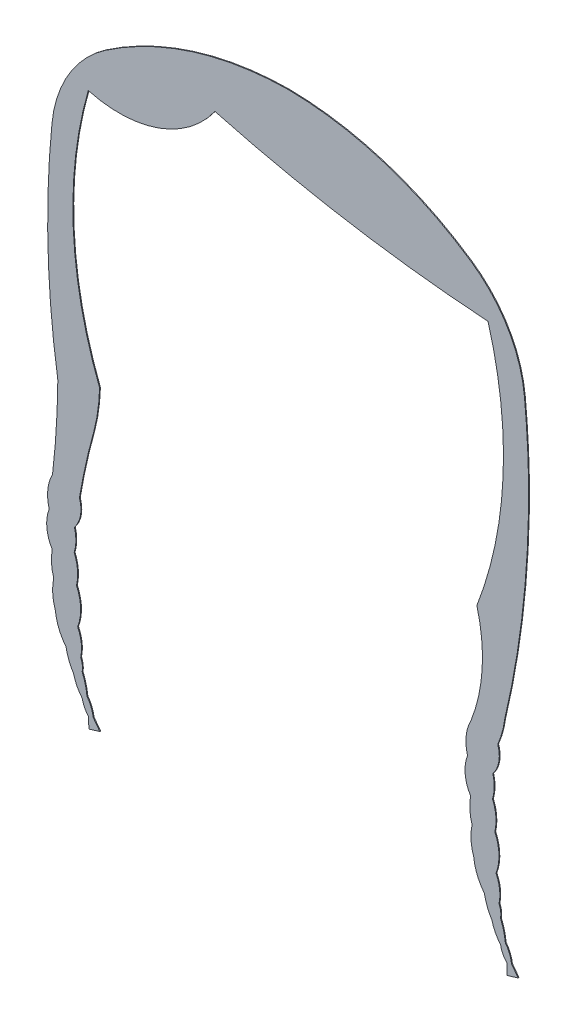
SolidWorks part; units mm, degrees
ref_plane "Alzado" through (0, 0, 0) normal (0, 0, 1) x (1, 0, 0)
ref_plane "Planta" through (0, 0, 0) normal (0, 1, 0) x (1, 0, 0)
ref_plane "Vista lateral" through (0, 0, 0) normal (1, 0, 0) x (0, 0, -1)
sketch "Model" plane through (0, 0, 0) normal (0, 0, 1) x (1, 0, 0)
  line L0 (83.9563, -17.167) -> (84.0154, -18.4772)
  line L1 (84.0154, -18.4772) -> (85.3366, -18.0776)
  line L2 (85.3366, -18.0776) -> (84.5382, -17.0083)
  line L3 (33.3554, -16.6534) -> (33.4145, -17.9637)
  line L4 (33.4145, -17.9637) -> (34.7357, -17.5641)
  line L5 (34.7357, -17.5641) -> (33.9374, -16.4947)
  arc A0 (79.7631, -4.8155) -> (79.9615, -8.08) centre (85.6296, -6.0972) ccw
  arc A1 (79.9615, -8.08) -> (81.2451, -11.2392) centre (85.9689, -7.4796) ccw
  arc A2 (81.2451, -11.2392) -> (82.1597, -13.5925) centre (87.7092, -10.0813) ccw
  arc A3 (82.1597, -13.5925) -> (83.2073, -15.6555) centre (87.0868, -12.388) ccw
  arc A4 (83.2073, -15.6555) -> (83.9563, -17.167) centre (86.1449, -15.141) ccw
  arc A5 (84.5382, -17.0083) -> (83.7865, -15.172) centre (80.6062, -17.5459) ccw
  arc A6 (83.7865, -15.172) -> (83.1987, -12.882) centre (75.7316, -16.0192) ccw
  arc A7 (83.1987, -12.882) -> (83.0211, -11.4509) centre (80.7624, -12.4576) ccw
  arc A8 (83.0211, -11.4509) -> (82.6546, -8.4482) centre (78.5154, -10.4772) ccw
  arc A9 (82.6546, -8.4482) -> (82.5111, -4.1773) centre (77.4881, -6.4838) ccw
  arc A10 (82.5111, -4.1773) -> (82.2345, -0.8781) centre (77.3398, -2.9497) ccw
  arc A11 (82.2345, -0.8781) -> (82.268, 1.804) centre (77.4744, 0.5228) ccw
  arc A12 (82.268, 1.804) -> (82.8651, 5.1538) centre (79.5154, 4.0228) ccw
  arc A13 (82.8651, 5.1538) -> (83.7243, 8.2948) centre (71.8523, 9.8543) ccw
  arc A14 (83.7243, 8.2948) -> (86.5847, 35.0224) centre (-22.8044, 33.2124) ccw
  arc A15 (86.5847, 35.0224) -> (86.0882, 43.2386) centre (-18.7575, 32.7793) ccw
  arc A16 (86.0882, 43.2386) -> (79.6155, 54.1408) centre (71.1622, 41.7496) ccw
  arc A17 (79.6155, 54.1408) -> (57.5166, 61.0841) centre (57.1104, 21.1518) ccw
  arc A18 (57.5166, 61.0841) -> (35.4178, 54.1408) centre (57.9228, 21.1518) ccw
  arc A19 (35.4178, 54.1408) -> (28.9451, 43.2386) centre (43.871, 41.7496) ccw
  arc A20 (28.9451, 43.2386) -> (29.6548, 16.7257) centre (133.7908, 32.7793) ccw
  arc A21 (29.0154, 6.5228) -> (29.6548, 16.7257) centre (-64.9236, 17.5318) ccw
  arc A22 (29.0154, 6.5228) -> (28.6101, 2.6863) centre (33.6016, 4.0987) ccw
  arc A23 (28.6101, 2.6863) -> (28.9787, -1.3635) centre (32.9145, 1.0363) ccw
  arc A24 (28.9787, -1.3635) -> (29.1622, -4.3019) centre (34.9782, -2.4637) ccw
  arc A25 (29.1622, -4.3019) -> (29.3607, -7.5664) centre (35.0287, -5.5836) ccw
  arc A26 (29.3607, -7.5664) -> (30.6442, -10.7256) centre (35.368, -6.966) ccw
  arc A27 (30.6442, -10.7256) -> (31.5588, -13.0789) centre (37.1083, -9.5677) ccw
  arc A28 (31.5588, -13.0789) -> (32.6064, -15.142) centre (36.486, -11.8745) ccw
  arc A29 (32.6064, -15.142) -> (33.3554, -16.6534) centre (35.5441, -14.6275) ccw
  arc A30 (33.9374, -16.4947) -> (33.1856, -14.6584) centre (30.0053, -17.0324) ccw
  arc A31 (33.1856, -14.6584) -> (32.5978, -12.3685) centre (25.1307, -15.5056) ccw
  arc A32 (32.5978, -12.3685) -> (32.4203, -10.9373) centre (30.1615, -11.9441) ccw
  arc A33 (32.4203, -10.9373) -> (32.0537, -7.9346) centre (27.9145, -9.9637) ccw
  arc A34 (32.0537, -7.9346) -> (31.9103, -3.6637) centre (26.8873, -5.9703) ccw
  arc A35 (31.9103, -3.6637) -> (31.6336, -0.3645) centre (26.7389, -2.4362) ccw
  arc A36 (31.6336, -0.3645) -> (31.6672, 2.3176) centre (26.8736, 1.0363) ccw
  arc A37 (31.6672, 2.3176) -> (32.2643, 5.6674) centre (28.9145, 4.5363) ccw
  arc A38 (34.0154, 13.5228) -> (32.2643, 5.6674) centre (107.7917, -7.0463) ccw
  arc A39 (34.0154, 13.5228) -> (34.7063, 18.416) centre (12.9916, 18.9869) ccw
  arc A40 (33.338, 48.8854) -> (34.7063, 18.416) centre (79.1984, 35.6795) ccw
  arc A41 (33.338, 48.8854) -> (48.6572, 54.357) centre (37.0741, 62.6062) ccw
  arc A42 (48.6572, 54.357) -> (81.6951, 48.8859) centre (93.0863, 220.1615) ccw
  arc A43 (80.3383, 18.4454) -> (81.6951, 48.8859) centre (35.8348, 35.6795) ccw
  arc A44 (79.6162, 6.0092) -> (80.3383, 18.4454) centre (61.2627, 13.314) ccw
  arc A45 (79.6162, 6.0092) -> (79.211, 2.1727) centre (84.2024, 3.5851) ccw
  arc A46 (79.211, 2.1727) -> (79.5795, -1.8771) centre (83.5154, 0.5228) ccw
  arc A47 (79.5795, -1.8771) -> (79.7631, -4.8155) centre (85.5791, -2.9772) ccw
extrude "Saliente-Extruir1" add sketch "Model" along normal blind 0.1
